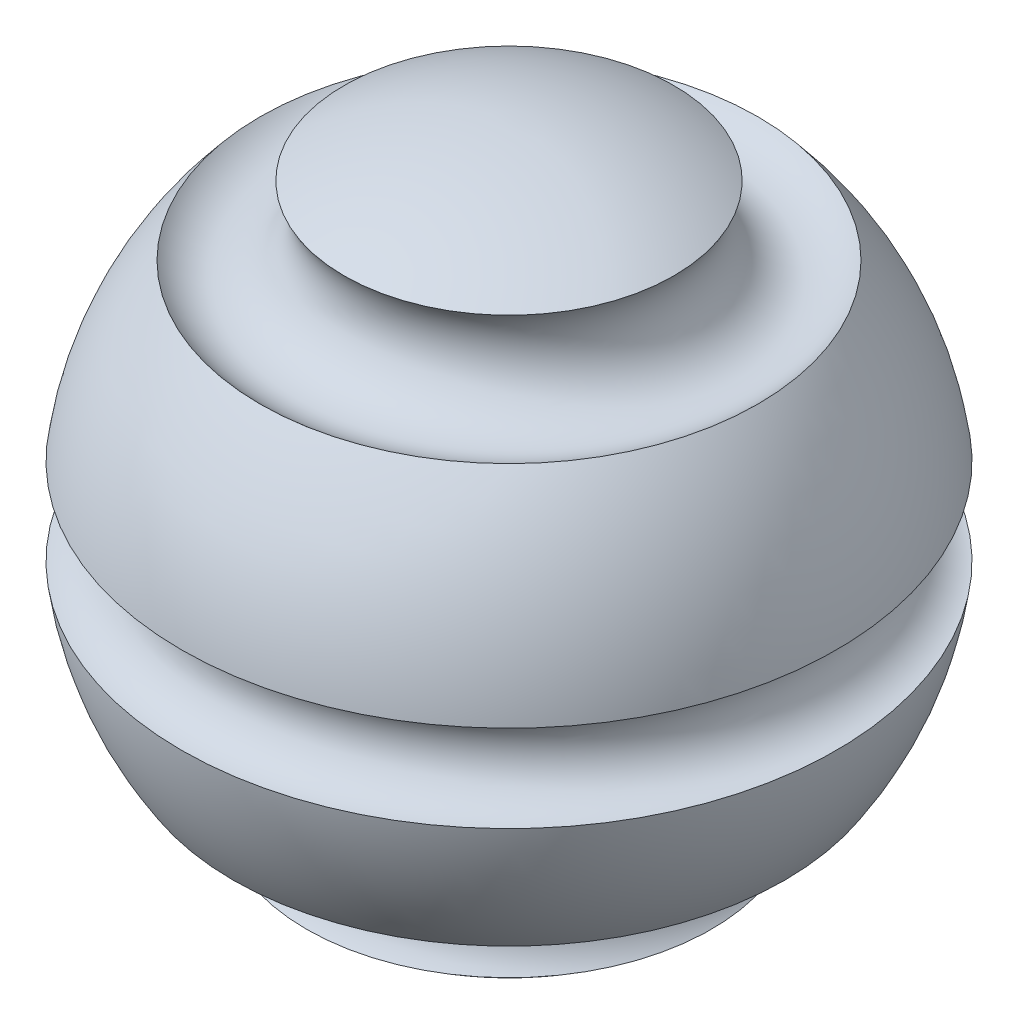
SolidWorks part; units mm, degrees
ref_plane "Front Plane" through (0, 0, 0) normal (0, 0, 1) x (1, 0, 0)
ref_plane "Top Plane" through (0, 0, 0) normal (0, 1, 0) x (1, 0, 0)
ref_plane "Right Plane" through (0, 0, 0) normal (1, 0, 0) x (0, 0, -1)
sketch "Sketch1" plane through (0, 0, 0) normal (0, 0, 1) x (1, 0, 0)
  line L0 (0, 10) -> (0, -10)
  arc A0 (0, 10) -> (-4.9927, 8.6644) centre (0, 0) ccw
  arc A1 (-7.5364, 6.5729) -> (-4.9927, 8.6644) centre (-6.3512, 7.7241) ccw
  arc A2 (-9.913, -1.3162) -> (-9.913, 1.3162) centre (-10, 0) ccw
  arc A3 (-6.1278, -7.9025) -> (-8.3478, -5.5059) centre (-7.3363, -6.7955) ccw
  arc A4 (-7.5364, 6.5729) -> (-9.913, 1.3162) centre (0, 0) ccw
  arc A5 (-9.913, -1.3162) -> (-8.3478, -5.5059) centre (0, 0) ccw
  arc A6 (-6.1278, -7.9025) -> (0, -10) centre (0, 0) ccw
  dimension "D1" = 10
revolve "Revolve1" add sketch "Sketch1" angle 360 about L0
